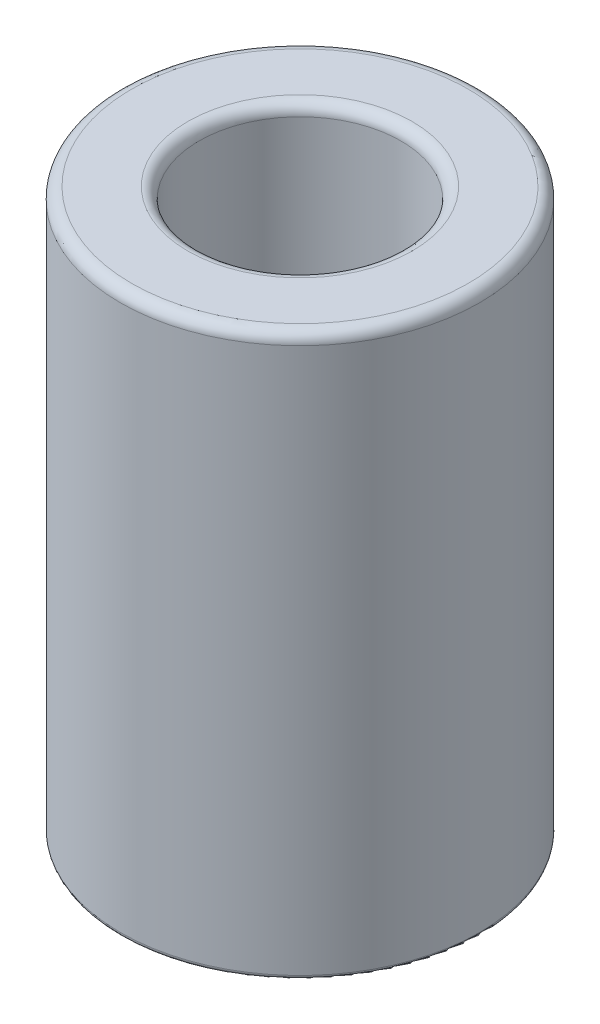
SolidWorks part; units mm, degrees
ref_plane "Front Plane" through (0, 0, 0) normal (0, 0, 1) x (1, 0, 0)
ref_plane "Top Plane" through (0, 0, 0) normal (0, 1, 0) x (1, 0, 0)
ref_plane "Right Plane" through (0, 0, 0) normal (1, 0, 0) x (0, 0, -1)
sketch "Sketch2" plane through (0, 0, 0) normal (0, 1, 0) x (1, 0, 0)
  circle A0 centre (0, 0) radius 8
  dimension "D1" = 16
extrude "Boss-Extrude1" add sketch "Sketch2" along normal blind 25
sketch "Sketch3" plane through (0, 25, 0) normal (0, 1, 0) x (1, 0, 0)
  circle A0 centre (0, 0) radius 4.5
  dimension "D1" = 9
extrude "Cut-Extrude1" cut sketch "Sketch3" against normal blind 15.13
sketch "Sketch4" plane through (0, 9.87, 0) normal (0, 1, 0) x (1, 0, 0)
  circle A0 centre (0, 0) radius 2.5
  dimension "D1" = 5
extrude "Cut-Extrude2" cut sketch "Sketch4" against normal through all
fillet "Fillet1" radius 0.5 1 edges at (0, 25, 8)
fillet "Fillet2" radius 0.5 1 edges at (0, 25, 4.5)
chamfer "Chamfer1" distance 0.5 angle 45 2 edges at (0, 0, 2.5) (0, 9.87, 2.5)
fillet "Fillet3" radius 0.2 1 edges at (0, 0, 8)
